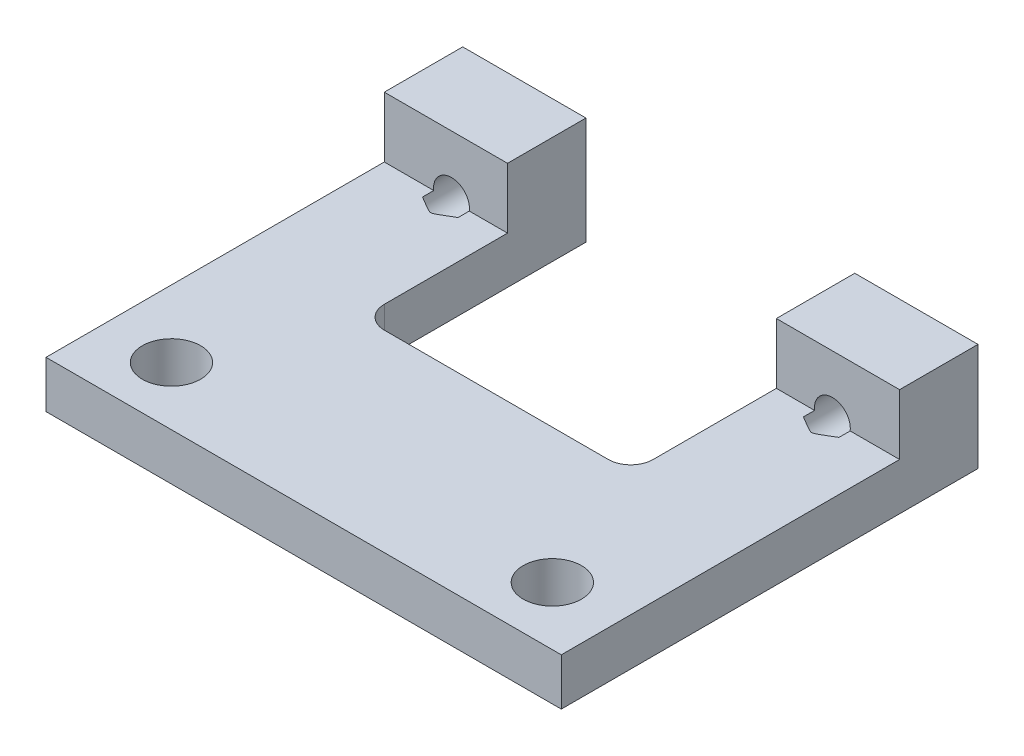
SolidWorks part; units mm, degrees
ref_plane "Front Plane" through (0, 0, 0) normal (0, 0, 1) x (1, 0, 0)
ref_plane "Top Plane" through (0, 0, 0) normal (0, 1, 0) x (1, 0, 0)
ref_plane "Right Plane" through (0, 0, 0) normal (1, 0, 0) x (0, 0, -1)
sketch "Sketch1" plane through (0, 0, 0) normal (0, 1, 0) x (1, 0, 0)
  line L1 (-11.5, 9.3) -> (11.5, 9.3)
  line L2 (-11.5, 9.3) -> (-11.5, -9.3)
  line L3 (-11.5, -9.3) -> (11.5, -9.3)
  line L4 (11.5, 9.3) -> (11.5, -9.3)
  line L5 (-11.5, 9.3) -> (11.5, -9.3) construction
  line L6 (-11.5, -9.3) -> (11.5, 9.3) construction
  point P0 (0, 0)
  dimension "D1" = 23
  dimension "D2" = 18.6
extrude "Boss-Extrude1" add sketch "Sketch1" along normal blind 4.8
sketch "Sketch2" plane through (11.5, 0, 0) normal (1, 0, 0) x (0, 0, -1)
  line L0 (9.3, 4.8) -> (9.3, 0) construction
  line L1 (-9.3, 4.8) -> (5.8, 4.8)
  line L2 (-9.3, 4.8) -> (-9.3, 2.1)
  line L3 (-9.3, 2.1) -> (5.8, 2.1)
  line L4 (5.8, 4.8) -> (5.8, 2.1)
  dimension "D1" = 2.7
  dimension "D2" = 3.5
extrude "Cut-Extrude1" cut sketch "Sketch2" against normal blind 27.8
sketch "Sketch3" plane through (0, 0, 0) normal (0, -1, 0) x (1, 0, 0)
  line L0 (11.5, -9.3) -> (-11.5, -9.3) construction
  line L1 (-6, -9.3) -> (6, -9.3)
  line L2 (-6, -9.3) -> (-6, 0.7)
  line L3 (-6, 0.7) -> (6, 0.7)
  line L4 (6, -9.3) -> (6, 0.7)
  dimension "D1" = 10
  dimension "D2" = 12
  dimension "D3" = 6
extrude "Cut-Extrude2" cut sketch "Sketch3" against normal blind 27.8
sketch "Sketch4" plane through (0, 0, -9.3) normal (0, 0, -1) x (-1, 0, 0)
  line L0 (6, 0) -> (11.5, 0) construction
  circle A0 centre (-8.5, 2.2) radius 0.6636
  circle A1 centre (8.5, 2.2) radius 0.6636
  dimension "D1" = 17
  dimension "D3" = 2.2
  dimension "D2" = 8.5
hole_wizard "M2x0.4 Tapped Hole1" positions "Sketch6" profile "Sketch5" tap size "M2x0.4" standard "Ansi Metric"
sketch "Sketch6" plane through (0, 0, -9.3) normal (0, 0, -1) x (-1, 0, 0)
  point P0 (-8.5, 2.2)
  point P1 (8.5, 2.2)
sketch "Sketch5" plane through (8.5, 2.2, -9.3) normal (1, 0, 0) x (0, 1, 0)
  line L0 (0, 0) -> (0, 4.4807)
  line L1 (0, 4.4807) -> (0.8, 4)
  line L2 (0.8, 4) -> (0.8, 0)
  line L5 (0.8, 0) -> (0, 0)
  line L10 (0, 4.4807) -> (-0.8, 4) construction
  line L11 (0, -6.35) -> (0, 107.95) construction
  dimension "Tap Drill Dia." = 1.6
  dimension "Tap Drill Depth" = 4
  dimension "Drill Angle" = 118
cosmetic thread "Hole Thread1" parameters "D1"=4, "D2"=2
cosmetic thread "Hole Thread2" parameters "D1"=4, "D2"=2
sketch "Sketch7" plane through (0, 0, 0) normal (0, -1, 0) x (1, 0, 0)
  line L0 (-11.5, 9.3) -> (11.5, 9.3) construction
  circle A0 centre (-8.5, 6.7) radius 1.3
  circle A1 centre (8.5, 6.7) radius 1.3
  dimension "D1" = 2.6
  dimension "D2" = 2.6
  dimension "D3" = 2.6
  dimension "D4" = 8.5
  dimension "D5" = 8.5
extrude "Cut-Extrude3" cut sketch "Sketch7" against normal blind 27.8
fillet "Fillet1" radius 1 2 edges at (6, 1.05, 0.7) (-6, 1.05, 0.7)
